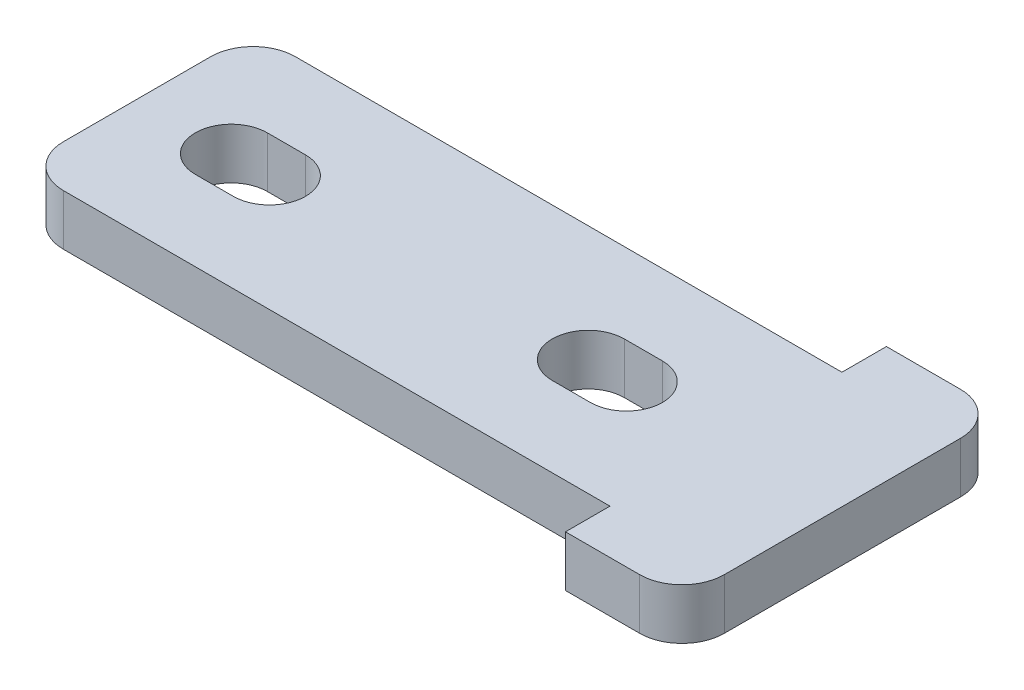
SolidWorks part; units mm, degrees
ref_plane "Front Plane" through (0, 0, 0) normal (0, 0, 1) x (1, 0, 0)
ref_plane "Top Plane" through (0, 0, 0) normal (0, 1, 0) x (1, 0, 0)
ref_plane "Right Plane" through (0, 0, 0) normal (1, 0, 0) x (0, 0, -1)
sketch "Sketch1" plane through (0, 0, 0) normal (0, 1, 0) x (1, 0, 0)
  line L1 (0, 0) -> (33.3, 0)
  line L2 (0, 0) -> (0, 15.15)
  line L3 (0, 15.15) -> (33.3, 15.15)
  line L4 (33.3, 0) -> (33.3, 15.15)
  line L9 (0, 0) -> (27.8, 0)
  line L10 (0, 0) -> (0, 2.1)
  line L11 (0, 2.1) -> (27.8, 2.1)
  line L12 (27.8, 0) -> (27.8, 2.1)
  line L13 (0, 15.15) -> (27.8, 15.15)
  line L14 (0, 15.15) -> (0, 13.05)
  line L15 (0, 13.05) -> (27.8, 13.05)
  line L16 (27.8, 15.15) -> (27.8, 13.05)
  line L17 (23.1, 7.575) -> (21.3, 7.575) construction
  line L18 (23.1, 5.875) -> (21.3, 5.875)
  line L19 (23.1, 9.275) -> (21.3, 9.275)
  line L20 (4.45, 7.575) -> (6.25, 7.575) construction
  line L21 (4.45, 9.275) -> (6.25, 9.275)
  line L22 (4.45, 5.875) -> (6.25, 5.875)
  arc A0 (23.1, 5.875) -> (23.1, 9.275) centre (23.1, 7.575) ccw
  arc A1 (21.3, 9.275) -> (21.3, 5.875) centre (21.3, 7.575) ccw
  arc A2 (4.45, 9.275) -> (4.45, 5.875) centre (4.45, 7.575) ccw
  arc A3 (6.25, 5.875) -> (6.25, 9.275) centre (6.25, 7.575) ccw
  point P14 (22.2, 7.575)
  point P22 (5.35, 7.575)
  dimension "D7" = 1.7
  dimension "D9" = 1.7
  dimension "D1" = 33.3
  dimension "D2" = 15.15
  dimension "D3" = 2.1
  dimension "D4" = 27.8
  dimension "D5" = 27.8
  dimension "D6" = 2.1
  dimension "D8" = 1.8
  dimension "D10" = 1.8
extrude "Boss-Extrude1" add sketch "Sketch1" against normal blind 2.4 contours L3 L16 L15 L2 L11 L12 L1 L4 A3 L22 A2 L21 A1 L19 A0 L18
fillet "Fillet1" radius 2 4 edges at (0, -1.2, -2.1) (0, -1.2, -13.05) (33.3, -1.2, 0) (33.3, -1.2, -15.15)
